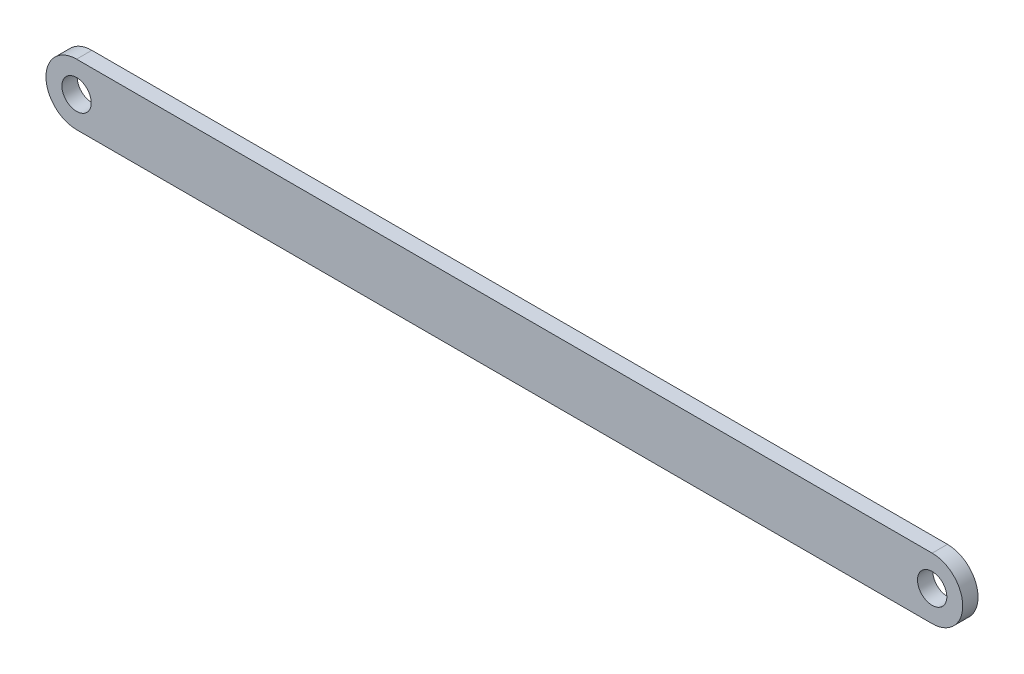
SolidWorks part; units mm, degrees
ref_plane "Front Plane" through (0, 0, 0) normal (0, 0, 1) x (1, 0, 0)
ref_plane "Top Plane" through (0, 0, 0) normal (0, 1, 0) x (1, 0, 0)
ref_plane "Right Plane" through (0, 0, 0) normal (1, 0, 0) x (0, 0, -1)
sketch "Sketch1" plane through (0, 0, 0) normal (0, 0, 1) x (1, 0, 0)
  line L1 (-88.9, -6.35) -> (88.9, -6.35)
  line L2 (-88.9, -6.35) -> (-88.9, 6.35) construction
  line L3 (-88.9, 6.35) -> (88.9, 6.35)
  line L4 (88.9, -6.35) -> (88.9, 6.35) construction
  line L5 (-88.9, -6.35) -> (88.9, 6.35) construction
  line L6 (-88.9, 6.35) -> (88.9, -6.35) construction
  arc A0 (88.9, 6.35) -> (88.9, -6.35) centre (88.9, 0) cw
  arc A1 (-88.9, 6.35) -> (-88.9, -6.35) centre (-88.9, 0) ccw
  circle A2 centre (-88.9, 0) radius 3.048
  circle A3 centre (88.9, 0) radius 3.048
  point P0 (0, 0)
  dimension "D3" = 6.096
  dimension "D4" = 6.096
  dimension "D1" = 177.8
  dimension "D2" = 12.7
extrude "Boss-Extrude1" add sketch "Sketch1" along normal blind 3.175
